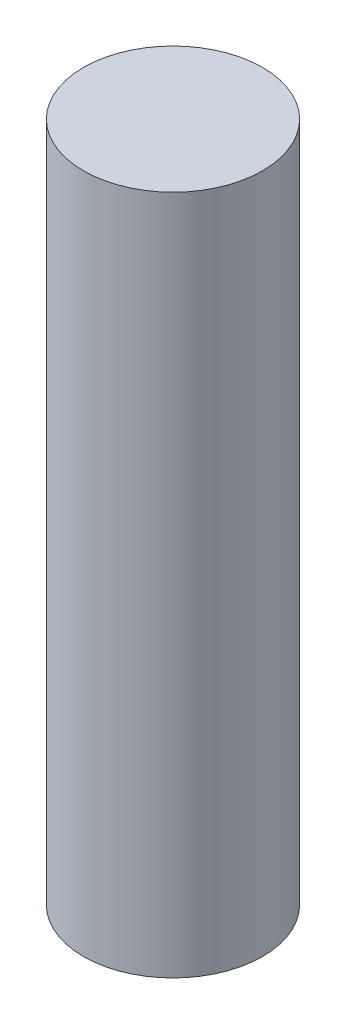
SolidWorks part; units mm, degrees
ref_plane "Front Plane" through (0, 0, 0) normal (0, 0, 1) x (1, 0, 0)
ref_plane "Top Plane" through (0, 0, 0) normal (0, 1, 0) x (1, 0, 0)
ref_plane "Right Plane" through (0, 0, 0) normal (1, 0, 0) x (0, 0, -1)
sketch "Sketch1" plane through (0, 0, 0) normal (0, 1, 0) x (1, 0, 0)
  circle A0 centre (0, 0) radius 1.5
  dimension "D1" = 3
extrude "Boss-Extrude1" add sketch "Sketch1" along normal blind 11.4 contours A0
